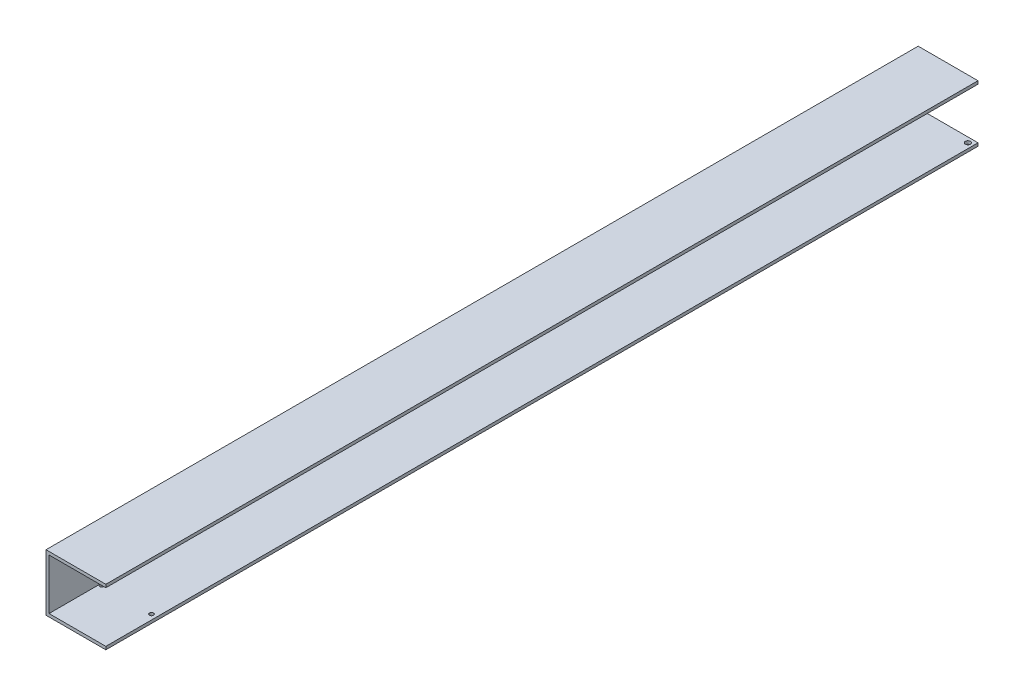
SolidWorks part; units mm, degrees
ref_plane "Piano frontale" through (0, 0, 0) normal (0, 0, 1) x (1, 0, 0)
ref_plane "Piano superiore" through (0, 0, 0) normal (0, 1, 0) x (1, 0, 0)
ref_plane "Piano destro" through (0, 0, 0) normal (1, 0, 0) x (0, 0, -1)
sketch "Schizzo1" plane through (0, 0, 0) normal (0, 0, 1) x (1, 0, 0)
  line L0 (28, -25) -> (28, -28)
  line L1 (-28, 25) -> (28, 25)
  line L2 (-28, 25) -> (-28, -25)
  line L3 (-28, -25) -> (28, -25)
  line L4 (28, -28) -> (-31, -28)
  line L5 (-28, 25) -> (28, -25) construction
  line L6 (-28, -25) -> (28, 25) construction
  line L7 (28, 25) -> (28, 28)
  line L8 (28, 28) -> (-31, 28)
  line L9 (-31, -28) -> (-31, 28)
  line L10 (28, -25.2903) -> (-31, 28) construction
  line L11 (28, 25.2903) -> (-31, -28) construction
  point P0 (0, 0)
  point P6 (0, 0)
  dimension "D1" = 56
  dimension "D2" = 50
  dimension "D3" = 56
  dimension "D4" = 3
  dimension "D5" = 56
  dimension "D6" = 3
extrude "Estrusione-Estrusione1" add sketch "Schizzo1" along normal blind 1005
sketch "Schizzo2" plane through (0, -28, 0) normal (0, -1, 0) x (-1, 0, 0)
  line L0 (31, -1005) -> (31, 0) construction
  line L1 (-28, -1005) -> (-28, 0) construction
  line L3 (31, -1005) -> (-28, -1005) construction
  circle A0 centre (-23, -955) radius 2
  circle A1 centre (26, -955) radius 2
  dimension "D3" = 4
  dimension "D4" = 4
  dimension "D1" = 5
  dimension "D2" = 5
  dimension "D5" = 50
  dimension "D6" = 50
extrude "Taglio-Estrusione1" cut sketch "Schizzo2" against normal blind 50
sketch "Schizzo3" plane through (0, -28, 0) normal (0, -1, 0) x (-1, 0, 0)
  line L0 (31, -1005) -> (31, 0) construction
  line L1 (-28, -1005) -> (-28, 0) construction
  line L2 (31, 0) -> (-28, 0) construction
  circle A0 centre (26, -150) radius 2.5
  circle A1 centre (-23, -150) radius 2.5
  dimension "D1" = 5
  dimension "D2" = 5
  dimension "D3" = 5
  dimension "D4" = 5
  dimension "D5" = 150
  dimension "D6" = 150
extrude "Taglio-Estrusione2" cut sketch "Schizzo3" against normal blind 50
sketch "Schizzo4" plane through (0, 28, 0) normal (0, 1, 0) x (1, 0, 0)
  line L0 (28, -1005) -> (28, 0) construction
  line L1 (28, 0) -> (-31, 0)
  line L2 (28, 0) -> (28, -145)
  line L3 (28, -145) -> (-31, -145)
  line L4 (-31, 0) -> (-31, -145)
  line L5 (28, 0) -> (-31, 0) construction
  line L6 (-31, -1005) -> (-31, 0) construction
  dimension "D1" = 145
extrude "Taglio-Estrusione3" cut sketch "Schizzo4" against normal blind 63
sketch "Schizzo8" plane through (-31, 0, 0) normal (-1, 0, 0) x (0, 0, 1)
  line L0 (145, -28) -> (145, 28) construction
  line L1 (1005, -28) -> (145, -28) construction
  circle A0 centre (175, -7) radius 2.5
  circle A1 centre (225, -7) radius 2.5
  dimension "D1" = 5
  dimension "D2" = 5
  dimension "D3" = 50
  dimension "D4" = 30
  dimension "D5" = 21
  dimension "D6" = 21
extrude "Taglio-Estrusione5" cut sketch "Schizzo8" against normal blind 10
